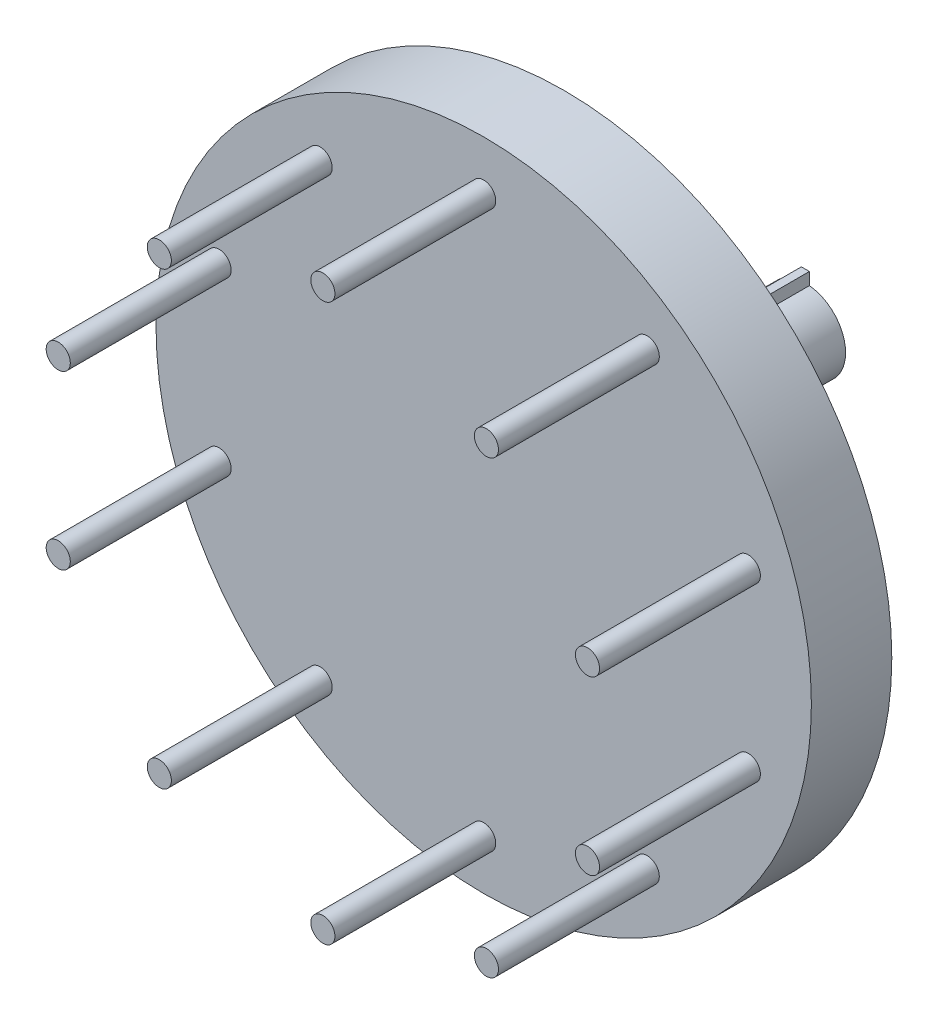
SolidWorks part; units mm, degrees
ref_plane "Front Plane" through (0, 0, 0) normal (0, 0, 1) x (1, 0, 0)
ref_plane "Top Plane" through (0, 0, 0) normal (0, 1, 0) x (1, 0, 0)
ref_plane "Right Plane" through (0, 0, 0) normal (1, 0, 0) x (0, 0, -1)
sketch "Sketch1" plane through (0, 0, 0) normal (0, 0, 1) x (1, 0, 0)
  circle A0 centre (0, 0) radius 34.6
  circle A1 centre (0, 34.6) radius 1.5
  circle A2 centre (20.3374, 27.992) radius 1.5
  circle A3 centre (32.9066, 10.692) radius 1.5
  circle A4 centre (32.9066, -10.692) radius 1.5
  circle A5 centre (20.3374, -27.992) radius 1.5
  circle A6 centre (0, -34.6) radius 1.5
  circle A7 centre (-20.3374, -27.992) radius 1.5
  circle A8 centre (-32.9066, -10.692) radius 1.5
  circle A9 centre (-32.9066, 10.692) radius 1.5
  circle A10 centre (-20.3374, 27.992) radius 1.5
  point P26 (0, 0)
  dimension "D1" = 69.2
  dimension "D2" = 3
  dimension "D3" = 10
extrude "Boss-Extrude1" add sketch "Sketch1" along normal blind 20 contours A0 A8 | A0 A9 | A0 A10 | A0 A1 | A0 A9 | A0 A8 | A0 A2 | A0 A7 | A0 A6 | A0 A5 | A0 A4 | A0 A3 | A0 A10 | A0 A7 | A0 A1 | A0 A2 | A0 A3 | A0 A4 | A0 A5 | A0 A6
sketch "Sketch2" plane through (0, 0, 0) normal (0, 0, -1) x (-1, 0, 0)
  circle A0 centre (0, 0) radius 40.75
  dimension "D1" = 81.5
extrude "Boss-Extrude2" add sketch "Sketch2" along normal blind 10
sketch "Sketch3" plane through (0, 0, -10) normal (0, 0, -1) x (-1, 0, 0)
  circle A0 centre (0, 0) radius 5
  dimension "D1" = 10
extrude "Boss-Extrude3" add sketch "Sketch3" along normal blind 30
sketch "Sketch4" plane through (0, 0, -40) normal (0, 0, -1) x (-1, 0, 0)
  line L0 (-0.5, 4.5) -> (0.5, 4.5)
  line L1 (0.5, 4.5) -> (0.5, 6.5)
  line L2 (0.5, 6.5) -> (-0.5, 6.5)
  line L3 (-0.5, 6.5) -> (-0.5, 4.5)
  line L4 (0, 0) -> (0, 5.7258) construction
  line L5 (-0.6294, 0) -> (1.1763, 0) construction
  line L6 (0.5, -6.5) -> (-0.5, -6.5)
  line L7 (0.5, -4.5) -> (0.5, -6.5)
  line L8 (-0.5, -4.5) -> (0.5, -4.5)
  line L9 (-0.5, -6.5) -> (-0.5, -4.5)
  dimension "D1" = 2
  dimension "D2" = 1
  dimension "D3" = 0.5
  dimension "D4" = 4.5
extrude "Boss-Extrude4" add sketch "Sketch4" against normal blind 30
